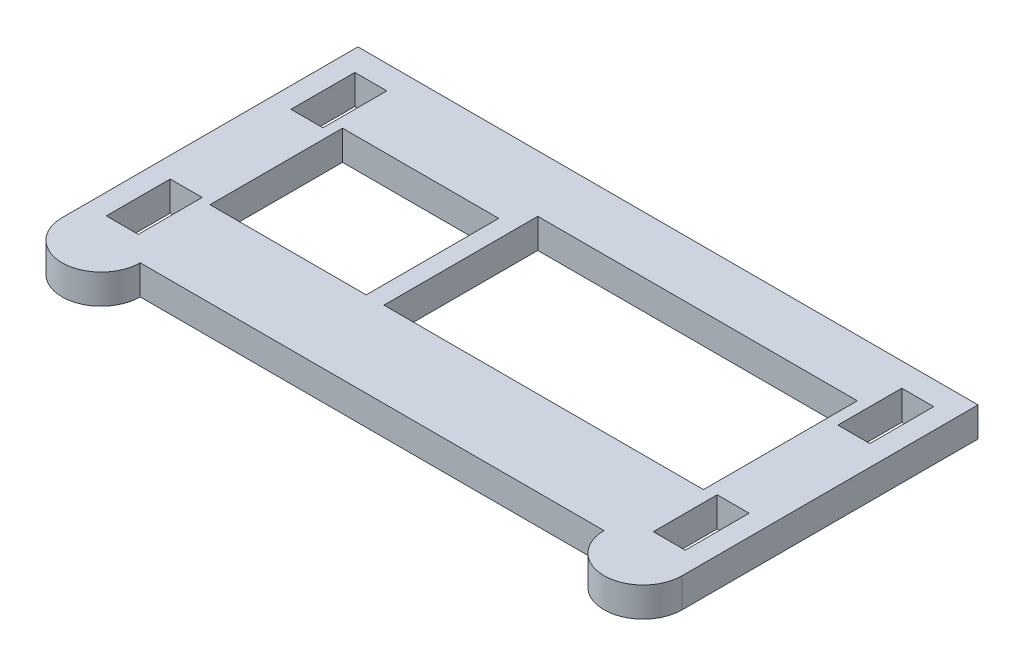
SolidWorks part; units mm, degrees
material "Custom Plastic"
ref_plane "Front Plane" through (0, 0, 0) normal (0, 0, 1) x (1, 0, 0)
ref_plane "Top Plane" through (0, 0, 0) normal (0, 1, 0) x (1, 0, 0)
ref_plane "Right Plane" through (0, 0, 0) normal (1, 0, 0) x (0, 0, -1)
sketch "Sketch1" plane through (0, 0, 0) normal (0, 1, 0) x (1, 0, 0)
  line L0 (0, 15.875) -> (0, -15.875) construction
  line L1 (-24.892, -15.875) -> (24.892, -15.875)
  line L2 (-33.274, -15.875) -> (-33.274, 15.875)
  line L3 (-33.274, 15.875) -> (33.274, 15.875)
  line L4 (33.274, -15.875) -> (33.274, 15.875)
  line L5 (-33.274, -15.875) -> (33.274, 15.875) construction
  line L6 (-33.274, 15.875) -> (33.274, -15.875) construction
  line L7 (31.0642, 13.335) -> (27.6352, 13.335)
  line L8 (31.0642, 13.335) -> (31.0642, 6.477)
  line L9 (31.0642, 6.477) -> (27.6352, 6.477)
  line L10 (27.6352, 13.335) -> (27.6352, 6.477)
  line L11 (31.0642, -6.477) -> (27.6352, -6.477)
  line L12 (31.0642, -6.477) -> (31.0642, -13.335)
  line L13 (31.0642, -13.335) -> (27.6352, -13.335)
  line L14 (27.6352, -6.477) -> (27.6352, -13.335)
  line L15 (-27.6352, -6.477) -> (-27.6352, -13.335)
  line L16 (-31.0642, -13.335) -> (-27.6352, -13.335)
  line L17 (-31.0642, -6.477) -> (-31.0642, -13.335)
  line L18 (-31.0642, -6.477) -> (-27.6352, -6.477)
  line L19 (-27.6352, 13.335) -> (-27.6352, 6.477)
  line L20 (-31.0642, 6.477) -> (-27.6352, 6.477)
  line L21 (-31.0642, 13.335) -> (-31.0642, 6.477)
  line L22 (-31.0642, 13.335) -> (-27.6352, 13.335)
  line L24 (-7.874, 9.779) -> (26.416, 9.779)
  line L25 (-7.874, 9.779) -> (-7.874, -6.731)
  line L26 (-7.874, -6.731) -> (26.416, -6.731)
  line L27 (26.416, 9.779) -> (26.416, -6.731)
  line L28 (-26.543, 7.493) -> (-9.779, 7.493)
  line L29 (-26.543, 7.493) -> (-26.543, -6.731)
  line L30 (-26.543, -6.731) -> (-9.779, -6.731)
  line L31 (-9.779, 7.493) -> (-9.779, -6.731)
  arc A0 (24.892, -15.875) -> (33.274, -15.875) centre (29.083, -15.875) ccw
  arc A1 (-24.892, -15.875) -> (-33.274, -15.875) centre (-29.083, -15.875) cw
  point P0 (0, 0)
  dimension "D13" = 4.191
  dimension "D1" = 66.548
  dimension "D2" = 31.75
  dimension "D3" = 2.2098
  dimension "D4" = 2.54
  dimension "D5" = 3.429
  dimension "D6" = 6.858
  dimension "D7" = 2.2098
  dimension "D8" = 2.54
  dimension "D9" = 16.51
  dimension "D10" = 9.144
  dimension "D11" = 6.858
  dimension "D12" = 34.29
  dimension "D14" = 14.224
  dimension "D15" = 6.731
  dimension "D16" = 16.764
  dimension "D17" = 9.144
extrude "Boss-Extrude1" add sketch "Sketch1" along normal blind 3.175
